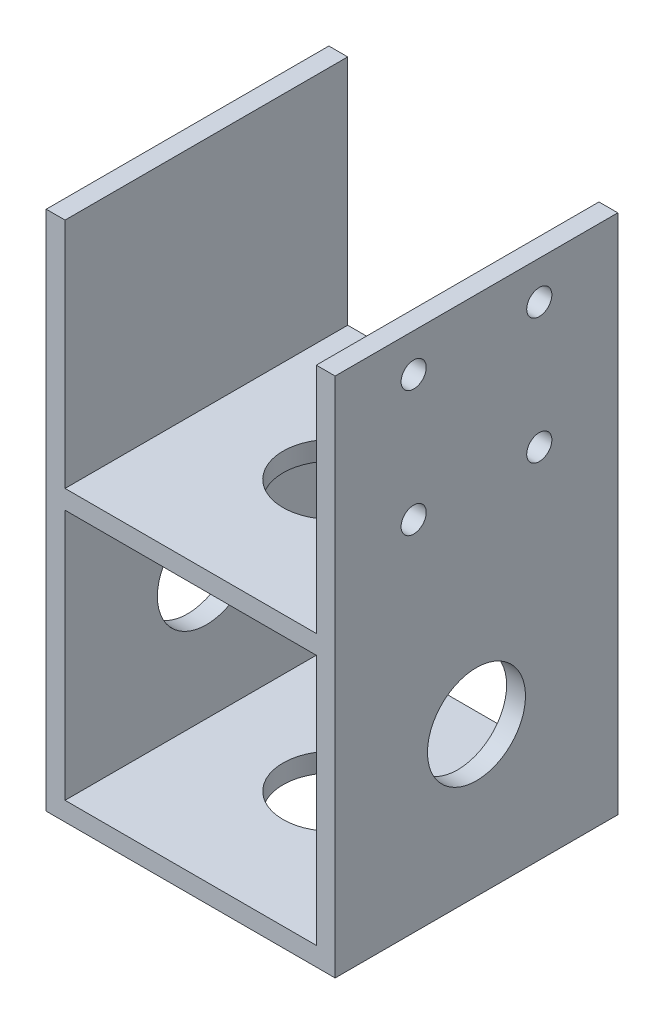
SolidWorks part; units mm, degrees
material "6061 Alloy"
ref_plane "Front Plane" through (0, 0, 0) normal (0, 0, 1) x (1, 0, 0)
ref_plane "Top Plane" through (0, 0, 0) normal (0, 1, 0) x (1, 0, 0)
ref_plane "Right Plane" through (0, 0, 0) normal (1, 0, 0) x (0, 0, -1)
sketch "Sketch1" plane through (0, 0, 0) normal (0, 1, 0) x (1, 0, 0)
  line L1 (23, -22.5) -> (-23, -22.5)
  line L2 (23, -22.5) -> (23, 22.5)
  line L3 (23, 22.5) -> (-23, 22.5)
  line L4 (-23, -22.5) -> (-23, 22.5)
  line L5 (23, -22.5) -> (-23, 22.5) construction
  line L6 (23, 22.5) -> (-23, -22.5) construction
  point P1 (0, 0)
  dimension "50" = 46
  dimension "D2" = 45
extrude "Boss-Extrude1" add sketch "Sketch1" along normal blind 3
sketch "Sketch5" plane through (0, 3, 0) normal (0, 1, 0) x (1, 0, 0)
  line L0 (-23, -22.5) -> (23, -22.5) construction
  line L1 (23, 22.5) -> (20, 22.5)
  line L2 (23, 22.5) -> (23, -22.5)
  line L3 (23, -22.5) -> (20, -22.5)
  line L4 (20, 22.5) -> (20, -22.5)
  line L7 (-23, 22.5) -> (-20, 22.5)
  line L8 (-23, 22.5) -> (-23, -22.5)
  line L9 (-23, -22.5) -> (-20, -22.5)
  line L10 (-20, 22.5) -> (-20, -22.5)
  dimension "D1" = 3
  dimension "D2" = 3
extrude "Boss-Extrude3" add sketch "Sketch5" along normal blind 35
sketch "Sketch9" plane through (0, 3, 0) normal (0, 1, 0) x (1, 0, 0)
  circle A0 centre (0, 0) radius 7.8
extrude "Cut-Extrude5" cut sketch "Sketch9" against normal blind 10
sketch "Sketch11" plane through (-23, 0, 0) normal (-1, 0, 0) x (0, 0, 1)
  line L0 (0, 0) -> (0, 38) construction
  line L5 (-22.5, 0) -> (22.5, 0) construction
  line L6 (-22.5, 38) -> (22.5, 38) construction
  line L7 (0, 38) -> (0, 19) construction
  line L8 (0, 19) -> (0, 28.5) construction
  line L9 (0, 28.5) -> (0, 19)
  circle A1 centre (0, 23.75) radius 7.8
extrude "Cut-Extrude8" cut sketch "Sketch11" against normal through all
sketch "Sketch12" plane through (0, 38, 0) normal (0, 1, 0) x (1, 0, 0)
  line L0 (-23, 22.5) -> (-20, 22.5)
  line L1 (-23, 22.5) -> (-23, -22.5)
  line L2 (-20, 22.5) -> (-20, -22.5)
  line L3 (-23, -22.5) -> (-20, -22.5)
  line L4 (20, 22.5) -> (23, 22.5)
  line L5 (20, 22.5) -> (20, -22.5)
  line L6 (23, 22.5) -> (23, -22.5)
  line L7 (20, -22.5) -> (23, -22.5)
  line L8 (20, -22.5) -> (23, -22.5) construction
  line L9 (-23, -22.5) -> (-20, -22.5) construction
extrude "Boss-Extrude4" add sketch "Sketch12" along normal blind 45
sketch "Sketch13" plane through (23, 0, 0) normal (1, 0, 0) x (0, 0, -1)
  line L0 (0, 83) -> (0, 31.55) construction
  line L1 (-22.5, 83) -> (22.5, 83) construction
  line L2 (0, 66.9557) -> (22.5, 66.9557) construction
  line L3 (22.5, 83) -> (22.5, 0) construction
  circle A0 centre (-10, 76.9557) radius 2
  circle A2 centre (0, 23.75) radius 7.8 construction
  circle A3 centre (10, 76.9557) radius 2
  circle A4 centre (10, 56.9557) radius 2
  circle A5 centre (-10, 56.9557) radius 2
  dimension "D3" = 4
  dimension "D1" = 10
  dimension "D2" = 10
extrude "Cut-Extrude9" cut sketch "Sketch13" against normal blind 10
ref_plane "Plane1" through (0, 23, 0) normal (0, 1, 0) x (1, 0, 0)
mirror "Mirror1" about plane through (0, 23, 0) normal (0, 1, 0) of "Cut-Extrude5", "Boss-Extrude1"
sketch "Sketch15" plane through (0, 83, 0) normal (0, 1, 0) x (1, 0, 0)
  line L0 (-23, 22.5) -> (23, 22.5)
  line L1 (-23, 22.5) -> (-23, -22.526)
  line L2 (23, 22.5) -> (23, -22.526)
  line L3 (-23, -22.526) -> (23, -22.526)
extrude "Boss-Extrude5" [suppressed] add sketch "Sketch15" along normal blind 3
sketch "Sketch16" [suppressed] plane through (0, 86, 0) normal (0, 1, 0) x (1, 0, 0)
  circle A0 centre (0, 0) radius 10.5
  circle A1 centre (0, 0) radius 13 construction
  circle A2 centre (0, 13) radius 1.5
  circle A3 centre (13, 0) radius 1.5
  circle A4 centre (0, -13) radius 1.5
  circle A5 centre (-13, 0) radius 1.5
  point P15 (0, 0)
  dimension "D1" = 21
  dimension "D2" = 3
  dimension "D4" = 26
  dimension "D3" = 4
extrude "Cut-Extrude10" [suppressed] cut sketch "Sketch16" against normal blind 3
